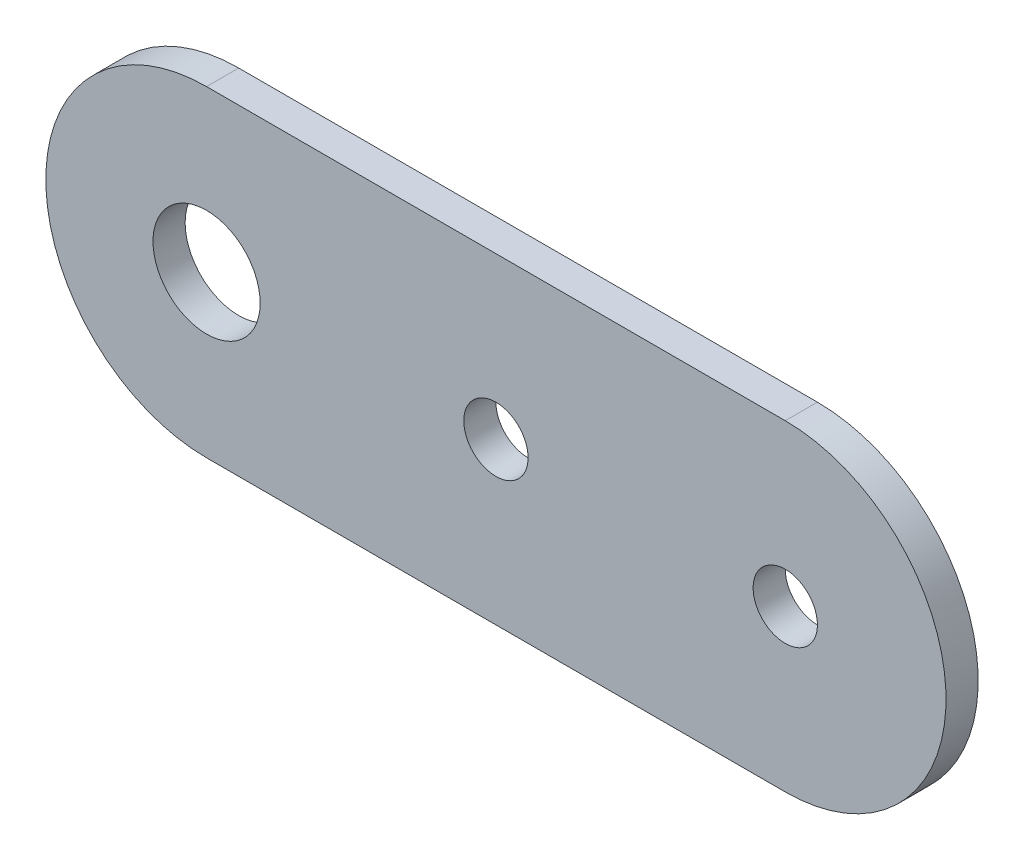
SolidWorks part; units mm, degrees
ref_plane "Front Plane" through (0, 0, 0) normal (0, 0, 1) x (1, 0, 0)
ref_plane "Top Plane" through (0, 0, 0) normal (0, 1, 0) x (1, 0, 0)
ref_plane "Right Plane" through (0, 0, 0) normal (1, 0, 0) x (0, 0, -1)
sketch "Sketch1" plane through (0, 0, 0) normal (0, 0, 1) x (1, 0, 0)
  line L0 (0, 15) -> (54, 15)
  line L1 (54, -15) -> (0, -15)
  arc A1 (0, -15) -> (0, 15) centre (0, 0) cw
  arc A6 (54, 15) -> (54, -15) centre (54, 0) cw
  point P1 (0, 0)
  point P3 (0, 0)
  point P7 (0, 0)
  point P8 (0, 0)
  dimension "D2" = 15
  dimension "D1" = 54
extrude "Boss-Extrude1" add sketch "Sketch1" along normal blind 3
sketch "Sketch2" plane through (0, 0, 3) normal (0, 0, 1) x (1, 0, 0)
  line L0 (-15, 0) -> (69, 0) construction
  circle A0 centre (0, 0) radius 5
  circle A2 centre (27, 0) radius 3
  arc A3 (54, -15) -> (54, 15) centre (54, 0) ccw construction
  arc A4 (0, 15) -> (0, -15) centre (0, 0) ccw construction
  circle A5 centre (54, 0) radius 3
  point P3 (75, 0)
  point P12 (0, 0)
  point P13 (47.0501, 0)
  point P15 (60, 0)
  point P18 (29.317, 0)
  dimension "D1" = 10
  dimension "D2" = 6
extrude "Cut-Extrude1" cut sketch "Sketch2" against normal up to surface (3 mm away) up to face at (27, 0, 0)
